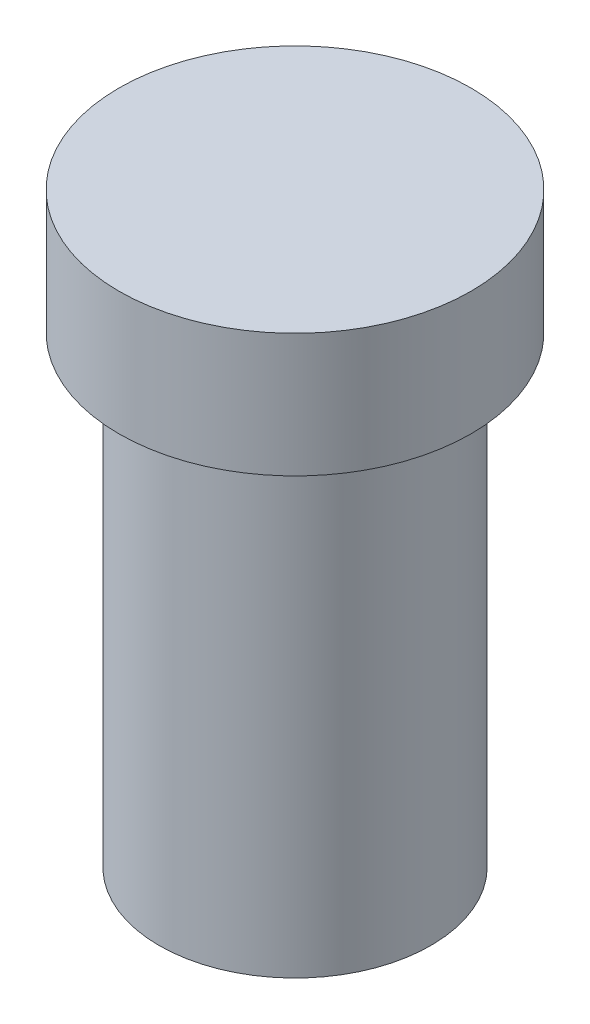
SolidWorks part; units mm, degrees
ref_plane "Front Plane" through (0, 0, 0) normal (0, 0, 1) x (1, 0, 0)
ref_plane "Top Plane" through (0, 0, 0) normal (0, 1, 0) x (1, 0, 0)
ref_plane "Right Plane" through (0, 0, 0) normal (1, 0, 0) x (0, 0, -1)
sketch "Sketch1" plane through (0, 0, 0) normal (0, 1, 0) x (1, 0, 0)
  circle A0 centre (0, 0) radius 22
  dimension "D1" = 44
extrude "Boss-Extrude1" add sketch "Sketch1" along normal mid plane 75
sketch "Sketch3" plane through (0, 0, 0) normal (1, 0, 0) x (0, 0, -1)
  line L0 (0, 37.5) -> (0, -37.5) construction
  dimension "D1" = 75
sketch "Sketch4" plane through (0, 37.5, 0) normal (0, 1, 0) x (1, 0, 0)
  circle A0 centre (0, 0) radius 28.5
  dimension "D1" = 57
extrude "Boss-Extrude2" add sketch "Sketch4" along normal blind 20
